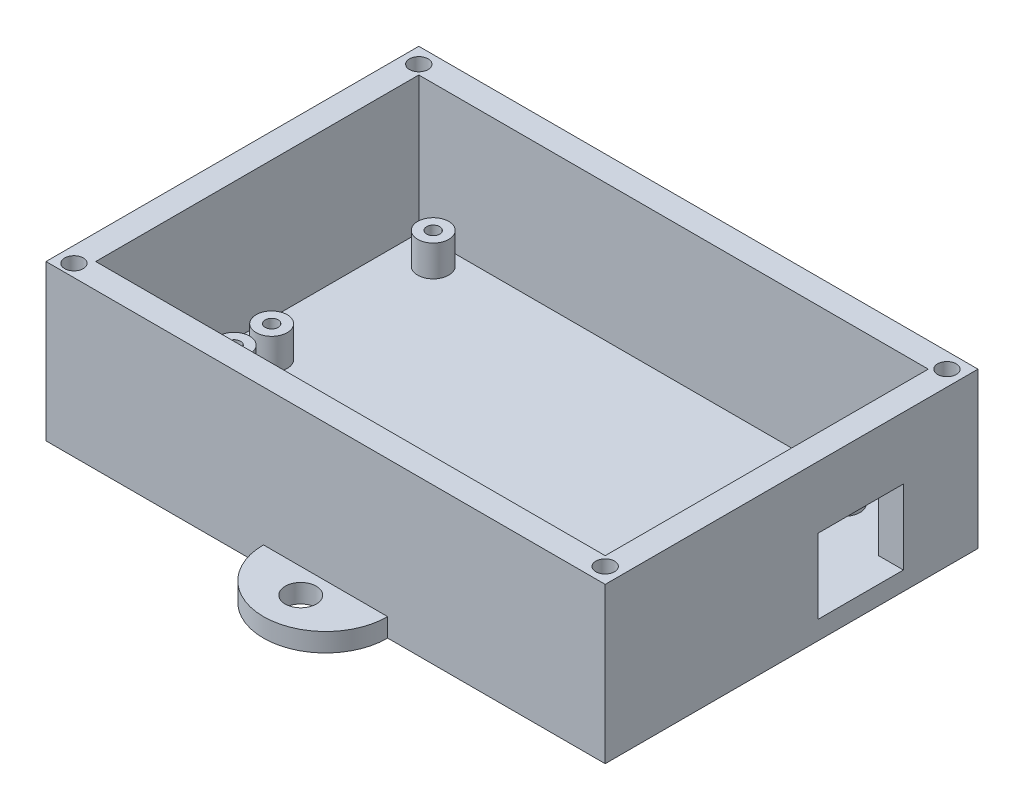
SolidWorks part; units mm, degrees
ref_plane "Front Plane" through (0, 0, 0) normal (0, 0, 1) x (1, 0, 0)
ref_plane "Top Plane" through (0, 0, 0) normal (0, 1, 0) x (1, 0, 0)
ref_plane "Right Plane" through (0, 0, 0) normal (1, 0, 0) x (0, 0, -1)
sketch "Sketch1" plane through (0, 0, 0) normal (0, 1, 0) x (1, 0, 0)
  line L0 (-45, 30) -> (-10, 30)
  line L5 (-45, 30) -> (45, -30) construction
  line L6 (-45, -30) -> (45, 30) construction
  line L7 (10, 30) -> (45, 30)
  line L8 (45, -30) -> (10, -30)
  line L9 (-10, -30) -> (-45, -30)
  line L18 (-45, 30) -> (-45, -30)
  line L19 (45, -30) -> (45, 30)
  arc A10 (-10, 30) -> (10, 30) centre (0, 30) cw
  arc A11 (10, -30) -> (-10, -30) centre (0, -30) cw
  circle A12 centre (0, 34) radius 2.5
  circle A13 centre (0, -34) radius 2.5
  point P0 (0, 0)
  dimension "D3" = 4
  dimension "D4" = 5
  dimension "D5" = 4
  dimension "D1" = 90
  dimension "D2" = 60
extrude "Boss-Extrude1" add sketch "Sketch1" along normal blind 3
sketch "Sketch2" plane through (0, 3, 0) normal (0, 1, 0) x (1, 0, 0)
  line L0 (-45, -30) -> (45, -30) construction
  circle A0 centre (-35.1792, 22.4995) radius 2.5
  circle A1 centre (31, 22.4995) radius 2.5
  circle A2 centre (31, -3.5005) radius 2.5
  circle A3 centre (-35.1792, -3.5005) radius 2.5
  circle A4 centre (-35.2206, -9.5003) radius 2.5
  circle A5 centre (31, -9.5003) radius 2.5
  circle A6 centre (-35.3102, -22.5) radius 2.5
  circle A7 centre (31, -22.5) radius 2.5
  dimension "D1" = 5
  dimension "D3" = 26
  dimension "D2" = 7.5
  dimension "D5" = 6
  dimension "D7" = 13
extrude "Boss-Extrude2" add sketch "Sketch2" along normal blind 5
sketch "Sketch4" plane through (0, 8, 0) normal (0, 1, 0) x (1, 0, 0)
  circle A0 centre (-35.1792, 22.4995) radius 1.05
  circle A1 centre (31, 22.4995) radius 1.05
  circle A2 centre (31, -3.5005) radius 1.05
  circle A3 centre (31, -9.5003) radius 1.05
  circle A4 centre (-35.1792, -3.5005) radius 1.05
  circle A5 centre (-35.2206, -9.5003) radius 1.05
  circle A6 centre (-35.3102, -22.5) radius 1.05
  circle A7 centre (31, -22.5) radius 1.05
  dimension "D1" = 2.1
extrude "Cut-Extrude2" cut sketch "Sketch4" against normal blind 4.5
sketch "Sketch6" plane through (0, 3, 0) normal (0, 1, 0) x (1, 0, 0)
  line L9 (-45, 30) -> (45, 30)
  line L10 (-45, 30) -> (-45, -30)
  line L11 (-45, -30) -> (45, -30)
  line L12 (45, 30) -> (45, -30)
  line L13 (-41, 26) -> (41, 26)
  line L14 (-41, 26) -> (-41, -26)
  line L15 (-41, -26) -> (41, -26)
  line L16 (41, 26) -> (41, -26)
  dimension "D1" = 4
  dimension "D2" = 4
  dimension "D3" = 4
  dimension "D4" = 4
extrude "Boss-Extrude3" add sketch "Sketch6" along normal blind 22
sketch "Sketch7" plane through (41, 0, 0) normal (-1, 0, 0) x (0, 0, 1)
  line L0 (26, 3) -> (-26, 3) construction
  line L1 (-18, 3) -> (-4.25, 3)
  line L2 (-18, 3) -> (-18, 15)
  line L3 (-18, 15) -> (-4.25, 15)
  line L4 (-4.25, 3) -> (-4.25, 15)
  line L5 (-26, 25) -> (-26, 3) construction
  dimension "D1" = 12
  dimension "D2" = 13.75
  dimension "D3" = 8
extrude "Cut-Extrude3" cut sketch "Sketch7" against normal blind 20
sketch "Sketch8" plane through (0, 25, 0) normal (0, 1, 0) x (1, 0, 0)
  line L0 (-45, 30) -> (-45, -30) construction
  line L1 (45, 30) -> (-45, 30) construction
  line L2 (45, -30) -> (45, 30) construction
  line L3 (-45, -30) -> (45, -30) construction
  circle A0 centre (-42.5, 27.5) radius 1.5
  circle A1 centre (42.5, 27.5) radius 1.5
  circle A2 centre (-42.5, -28) radius 1.5
  circle A3 centre (42.5, -27.5) radius 1.5
  dimension "D1" = 3
  dimension "D6" = 2.5
  dimension "D2" = 2.5
  dimension "D3" = 2.5
  dimension "D4" = 2.5
  dimension "D5" = 2
  dimension "D7" = 2.5
  dimension "D8" = 2.5
  dimension "D9" = 2.5
extrude "Cut-Extrude4" cut sketch "Sketch8" against normal blind 10
sketch "Sketch10" plane through (-41, 0, 0) normal (1, 0, 0) x (0, 0, -1)
  line L0 (26, 3) -> (-26, 3) construction
  line L1 (-12.8003, 3) -> (-19.3003, 3)
  line L2 (-12.8003, 3) -> (-12.8003, 8.0055)
  line L3 (-12.8003, 8.0055) -> (-19.3003, 8.0055)
  line L4 (-19.3003, 3) -> (-19.3003, 8.0055)
  dimension "D1" = 6.5
  dimension "D2" = 2.25
extrude "Cut-Extrude5" cut sketch "Sketch10" against normal blind 10
